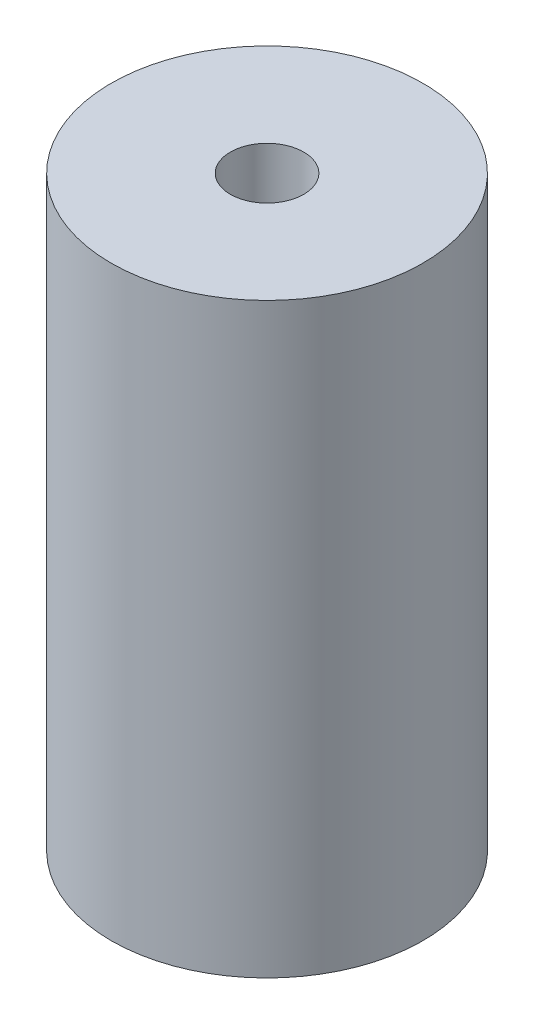
SolidWorks part; units mm, degrees
material "Rubber"
ref_plane "Front Plane" through (0, 0, 0) normal (0, 0, 1) x (1, 0, 0)
ref_plane "Top Plane" through (0, 0, 0) normal (0, 1, 0) x (1, 0, 0)
ref_plane "Right Plane" through (0, 0, 0) normal (1, 0, 0) x (0, 0, -1)
sketch "Sketch1" plane through (0, 0, 0) normal (0, 1, 0) x (1, 0, 0)
  circle A0 centre (0, 0) radius 6.35
  circle A1 centre (0, 0) radius 26.9875
extrude "Boss-Extrude1" add sketch "Sketch1" along normal blind 95.25 and the other way blind 6.35
